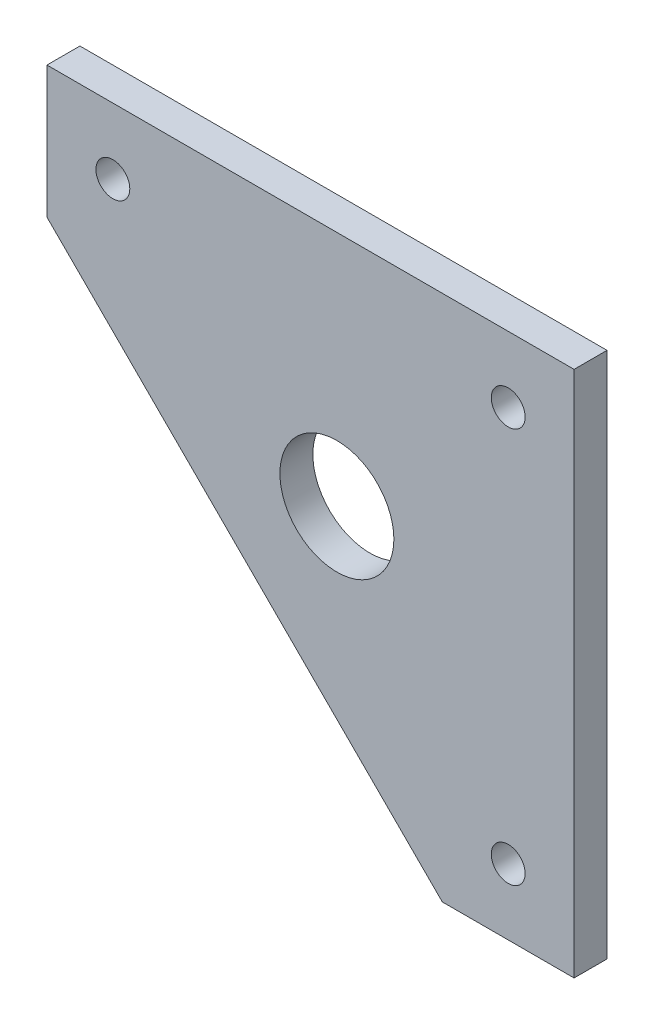
SolidWorks part; units mm, degrees
ref_plane "Front Plane" through (0, 0, 0) normal (0, 0, 1) x (1, 0, 0)
ref_plane "Top Plane" through (0, 0, 0) normal (0, 1, 0) x (1, 0, 0)
ref_plane "Right Plane" through (0, 0, 0) normal (1, 0, 0) x (0, 0, -1)
sketch "Sketch1" plane through (0, 0, 0) normal (0, 0, 1) x (1, 0, 0)
  line L0 (0, 0) -> (0, -62.6981) construction
  line L1 (0, 0) -> (-59.7893, 0) construction
  line L2 (-12.7, -12.7) -> (-12.7, -122.6401) construction
  line L3 (-12.7, -12.7) -> (-109.6721, -12.7) construction
  line L4 (12.7, 12.7) -> (-109.6721, 12.7) construction
  line L5 (12.7, 12.7) -> (12.7, -122.6401) construction
  line L6 (-88.9, 12.7) -> (-88.9, -12.7)
  line L7 (-88.9, -12.7) -> (-12.7, -88.9)
  line L8 (-12.7, -88.9) -> (12.7, -88.9)
  line L9 (-88.9, 12.7) -> (12.7, 12.7)
  line L10 (12.7, 12.7) -> (12.7, -88.9)
  line L12 (-50.165, -15.875) -> (-15.875, -15.875) construction
  line L13 (-50.165, -15.875) -> (-50.165, -50.165) construction
  line L14 (-50.165, -50.165) -> (-15.875, -50.165) construction
  line L15 (-15.875, -15.875) -> (-15.875, -50.165) construction
  line L16 (-50.165, -15.875) -> (-15.875, -50.165) construction
  line L17 (-50.165, -50.165) -> (-15.875, -15.875) construction
  circle A0 centre (-33.02, -33.02) radius 10.9855
  point P14 (-33.02, -33.02)
  dimension "D3" = 21.971
  dimension "D1" = 12.7
  dimension "D2" = 12.7
  dimension "D4" = 34.29
  dimension "D5" = 34.29
  dimension "D6" = 101.6
  dimension "D7" = 101.6
  dimension "D8" = 3.175
  dimension "D9" = 3.175
extrude "Boss-Extrude1" add sketch "Sketch1" along normal blind 6.35
hole_wizard "1/4 Clearance Hole1" positions "Sketch3" profile "Sketch2" hole size "1/4" standard "ANSI Inch" end condition through all
sketch "Sketch3" plane through (0, 0, 6.35) normal (0, 0, 1) x (1, 0, 0)
  point P0 (0, 0)
  point P3 (-76.2, 0)
  point P5 (0, -76.2)
  dimension "D1" = 76.2
  dimension "D2" = 76.2
sketch "Sketch2" plane through (0, 0, 6.35) normal (1, 0, 0) x (0, -1, 0)
  line L0 (0, 0) -> (0, 6.35)
  line L1 (0, 6.35) -> (3.2639, 6.35)
  line L2 (3.2639, 6.35) -> (3.2639, 0)
  line L5 (3.2639, 0) -> (0, 0)
  line L11 (0, -6.35) -> (0, 107.95) construction
  dimension "Thru Hole Dia." = 6.5278
  dimension "Thru Hole Depth" = 6.35
